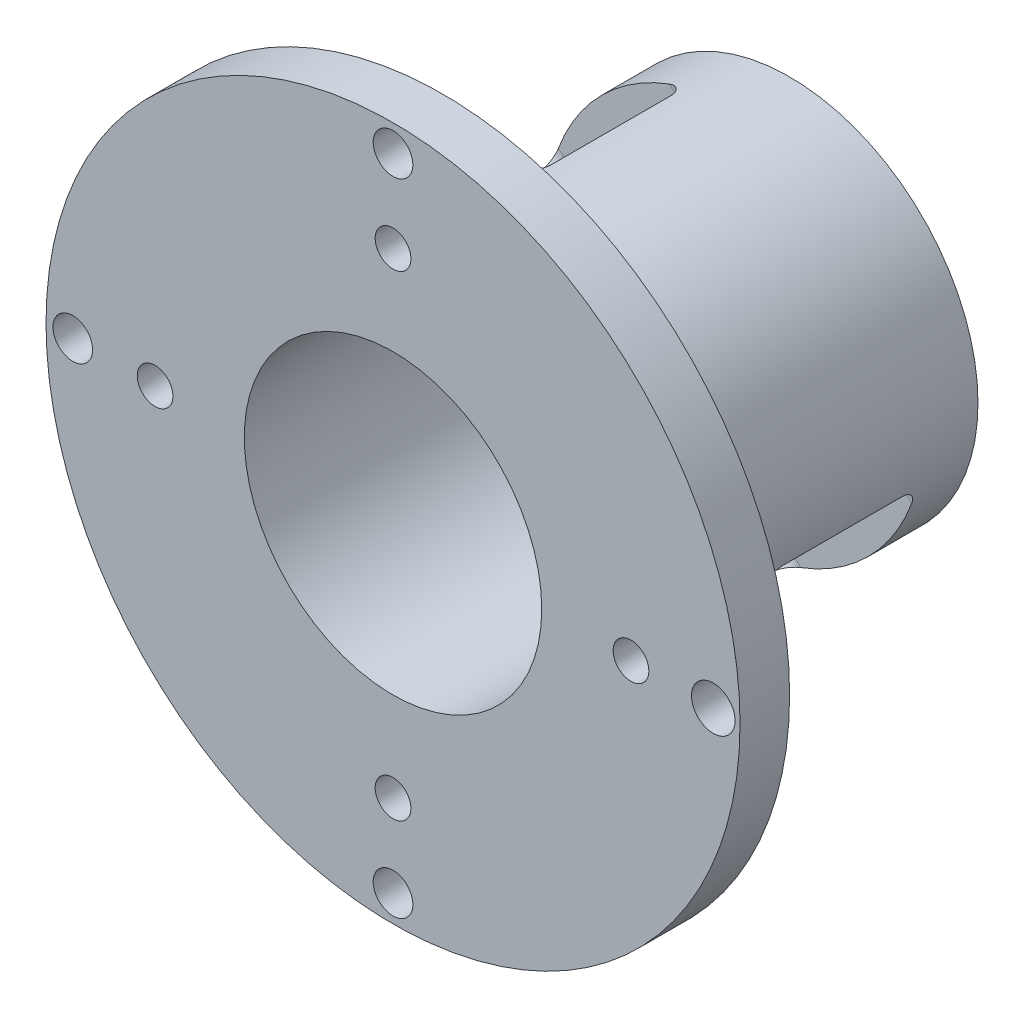
SolidWorks part; units mm, degrees
ref_plane "前视基准面" through (0, 0, 0) normal (0, 0, 1) x (1, 0, 0)
ref_plane "上视基准面" through (0, 0, 0) normal (0, 1, 0) x (1, 0, 0)
ref_plane "右视基准面" through (0, 0, 0) normal (1, 0, 0) x (0, 0, -1)
sketch "草图1" plane through (0, 0, 0) normal (0, 0, 1) x (1, 0, 0)
  line L0 (0, 35) -> (0, -35) construction
  line L1 (-35, 0) -> (35, 0) construction
  circle A0 centre (0, 0) radius 35
  circle A1 centre (0, 0) radius 4
extrude "凸台-拉伸1" add sketch "草图1" along normal blind 40
sketch "草图3" plane through (0, 0, 0) normal (0, 0, 1) x (1, 0, 0)
  circle A0 centre (0, 0) radius 35
  circle A1 centre (0, 0) radius 19
extrude "切除-拉伸1" cut sketch "草图3" along normal blind 35
sketch "草图4" plane through (0, 0, 40) normal (0, 0, 1) x (1, 0, 0)
  circle A0 centre (0, 0) radius 15
extrude "切除-拉伸2" cut sketch "草图4" against normal blind 33.5
sketch "草图6" plane through (0, 0, 0) normal (0, 0, 1) x (1, 0, 0)
  line L2 (-35, 0) -> (35, 0) construction
  line L3 (0, 35) -> (0, -35) construction
  circle A0 centre (-24, 0) radius 1.8
  circle A1 centre (0, -24) radius 1.8
  circle A2 centre (24, 0) radius 1.8
  circle A3 centre (0, 24) radius 1.8
  circle A4 centre (-32.3, 0) radius 2
  circle A5 centre (32.3, 0) radius 2.2
  circle A6 centre (0, 32.3) radius 2
  circle A7 centre (0, -32.3) radius 2
  dimension "D6" = 32.3
  dimension "D1" = 24
  dimension "D2" = 24
  dimension "D3" = 24
  dimension "D4" = 24
  dimension "D5" = 32.3
  dimension "D7" = 32.3
  dimension "D8" = 32.3
extrude "切除-拉伸3" cut sketch "草图6" along normal through all
sketch "草图7" plane through (0, 0, 0) normal (0, 0, -1) x (-1, 0, 0)
  line L0 (35, 0) -> (-35, 0) construction
  line L1 (0, 35) -> (0, -35) construction
  line L2 (0, 0) -> (-8.1317, -8.1317) construction
  line L3 (0, 0) -> (8.1317, 8.1317) construction
  line L4 (0, 0) -> (8.1317, -8.1317) construction
  line L5 (0, 0) -> (-8.1317, 8.1317) construction
  circle A0 centre (-9.5, 0) radius 1.5
  circle A1 centre (0, 8) radius 1.5
  circle A2 centre (9.5, 0) radius 1.5
  circle A3 centre (0, -8) radius 1.5
  circle A4 centre (-8.1317, -8.1317) radius 1.75
  circle A5 centre (-8.1317, 8.1317) radius 1.75
  circle A6 centre (8.1317, 8.1317) radius 1.75
  circle A7 centre (8.1317, -8.1317) radius 1.75
  dimension "D1" = 9.5
  dimension "D2" = 9.5
  dimension "D3" = 8
  dimension "D4" = 8
extrude "切除-拉伸4" cut sketch "草图7" against normal through all
sketch "草图8" plane through (0, 0, 0) normal (0, 0, -1) x (-1, 0, 0)
  line L1 (19.8458, -19.8458) -> (0, 0) construction
ref_plane "基准面1" through (0, 0, 0) normal (0.7071, -0.7071, 0) x (0.7071, 0.7071, 0)
sketch "草图9" plane through (0, 0, 0) normal (0.7071, -0.7071, 0) x (0.7071, 0.7071, 0)
  line L0 (0, 0) -> (0, 13) construction
  line L2 (-7.9133, 20.5) -> (7.9133, 20.5)
  line L3 (-9.4133, 19) -> (-9.4133, 7)
  line L4 (-7.9133, 5.5) -> (7.9133, 5.5)
  line L5 (9.4133, 19) -> (9.4133, 7)
  line L6 (-9.4133, 20.5) -> (9.4133, 5.5) construction
  line L7 (-9.4133, 5.5) -> (9.4133, 20.5) construction
  arc A0 (9.4133, 19) -> (7.9133, 20.5) centre (7.9133, 19) ccw
  arc A1 (9.4133, 7) -> (7.9133, 5.5) centre (7.9133, 7) cw
  arc A2 (-7.9133, 5.5) -> (-9.4133, 7) centre (-7.9133, 7) cw
  arc A3 (-9.4133, 19) -> (-7.9133, 20.5) centre (-7.9133, 19) cw
  dimension "D1" = 1.5
extrude "切除-拉伸5" cut sketch "草图9" against normal through all both and the other way through all
sketch "草图11" plane through (0, 0, 0) normal (0, 0, -1) x (-1, 0, 0)
  line L0 (0, 20.2858) -> (0, -16.9622) construction
  line L1 (-17.5536, 0) -> (20.6692, 0) construction
sketch "草图12" plane through (0, 0, 0) normal (0, 0, -1) x (-1, 0, 0)
  line L0 (-13, 0) -> (-13, -4) construction
  line L1 (-17.5536, 0) -> (20.6692, 0) construction
  line L2 (-13, 0) -> (-13, -4)
  line L3 (0, 0) -> (-13, 0) construction
  line L4 (-13, -4) -> (-10, -4)
  line L5 (-4, -10) -> (-4, -13)
  line L6 (-4, -13) -> (0, -13)
  line L7 (0, 0) -> (0, -13) construction
  line L8 (0, 0) -> (-16.6166, -16.6166) construction
  line L9 (0, 13) -> (-4, 13)
  line L10 (-13, 4) -> (-13, 0)
  line L11 (-10, 4) -> (-13, 4)
  line L12 (-4, 13) -> (-4, 10)
  line L13 (13, 0) -> (13, 4)
  line L14 (4, 13) -> (0, 13)
  line L15 (4, 10) -> (4, 13)
  line L16 (13, 4) -> (10, 4)
  line L17 (0, -13) -> (4, -13)
  line L18 (13, -4) -> (13, 0)
  line L19 (10, -4) -> (13, -4)
  line L20 (4, -13) -> (4, -10)
  circle A0 centre (0, 0) radius 19
  arc A1 (-4, -10) -> (-10, -4) centre (-10, -10) ccw
  arc A2 (-10, 4) -> (-4, 10) centre (-10, 10) ccw
  circle A3 centre (0, 0) radius 19
  arc A4 (4, 10) -> (10, 4) centre (10, 10) ccw
  circle A5 centre (0, 0) radius 19
  arc A6 (10, -4) -> (4, -10) centre (10, -10) ccw
  circle A7 centre (0, 0) radius 19
  point P13 (-4, -4)
  point P40 (0, 0)
  circle M5 centre (0, 8) radius 1.5
  circle M6 centre (9.5, 0) radius 1.5
  circle M7 centre (0, -8) radius 1.5
  circle M12 centre (-9.5, 0) radius 1.5
  circle M13 centre (0, 0) radius 4
  dimension "D1" = 45
  dimension "D2" = 6
  dimension "D3" = 4
extrude "切除-拉伸6" cut sketch "草图12" against normal blind 3 contours A6 L19 L18 L13 L16 A4 L15 L14 L9 L12 A2 L11 L10 L2 L4 A1 L5 L6 L17 L20 M6 M12 M13 M7 M5
